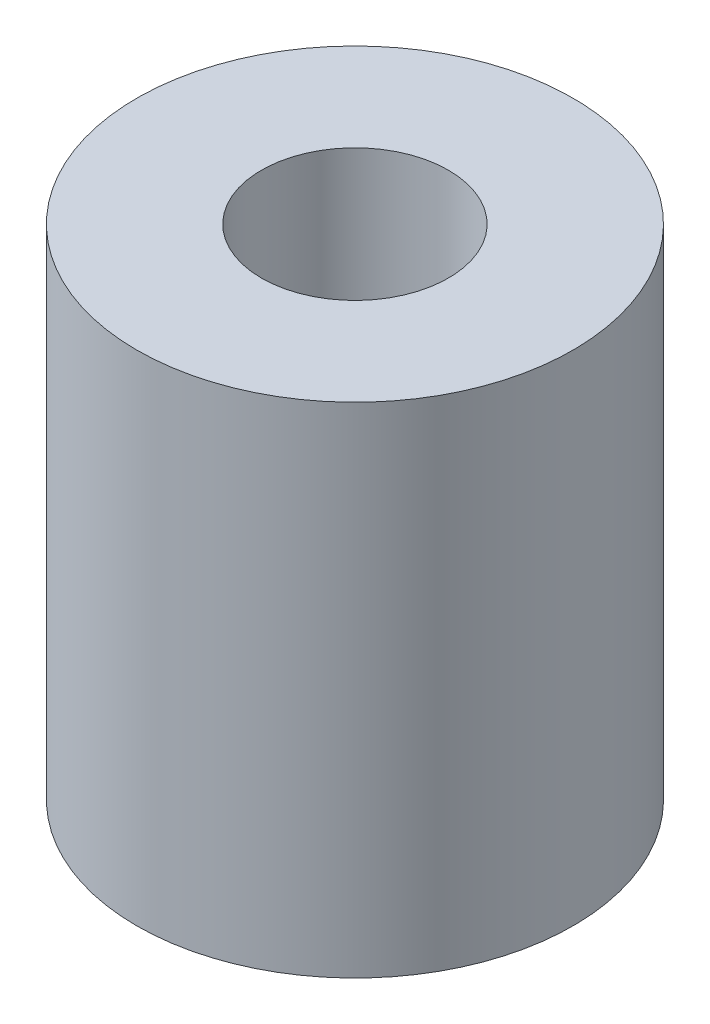
SolidWorks part; units mm, degrees
material "尼龙 101"
ref_plane "前视基准面" through (0, 0, 0) normal (0, 0, 1) x (1, 0, 0)
ref_plane "上视基准面" through (0, 0, 0) normal (0, 1, 0) x (1, 0, 0)
ref_plane "右视基准面" through (0, 0, 0) normal (1, 0, 0) x (0, 0, -1)
sketch "草图1" plane through (0, 0, 0) normal (0, 1, 0) x (1, 0, 0)
  circle A0 centre (0, 0) radius 3.5
  circle A1 centre (0, 0) radius 1.5
  dimension "D1" = 3
  dimension "D2" = 7
extrude "凸台-拉伸1" add sketch "草图1" along normal blind 8
